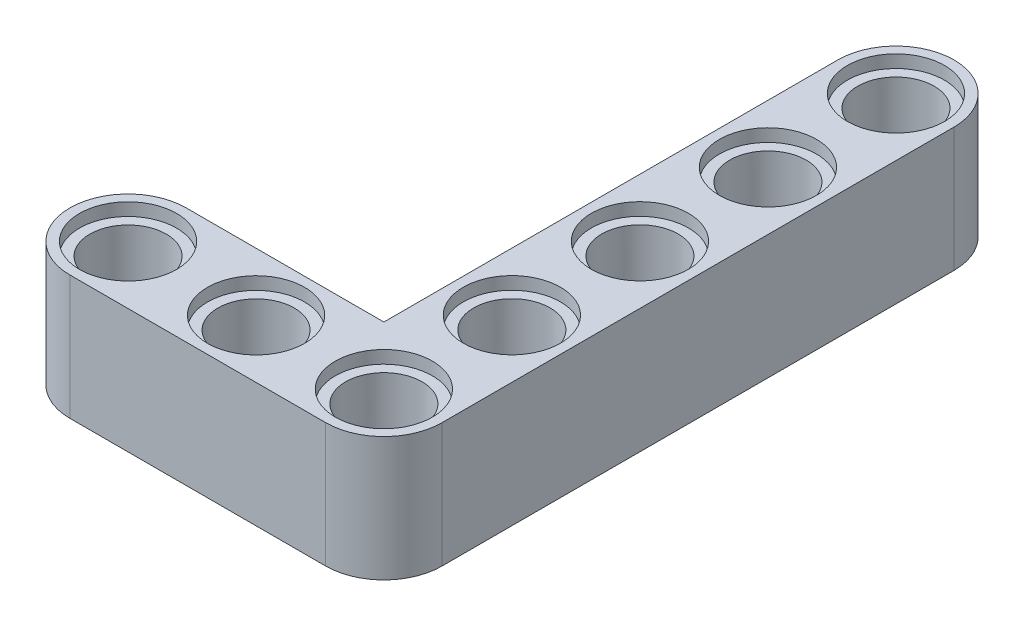
SolidWorks part; units mm, degrees
ref_plane "Front Plane" through (0, 0, 0) normal (0, 0, 1) x (1, 0, 0)
ref_plane "Top Plane" through (0, 0, 0) normal (0, 1, 0) x (1, 0, 0)
ref_plane "Right Plane" through (0, 0, 0) normal (1, 0, 0) x (0, 0, -1)
sketch "Sketch1" plane through (0, 0, 0) normal (0, 1, 0) x (1, 0, 0)
  line L0 (-39.0124, -18.5406) -> (-22.9465, -18.5406) construction
  line L1 (-39.0124, -14.8906) -> (-26.5965, -14.8906)
  line L2 (-39.0124, -22.1906) -> (-22.9465, -22.1906)
  line L3 (-22.9465, -18.5406) -> (-22.9465, 13.6194) construction
  line L4 (-26.5965, -14.8906) -> (-26.5965, 13.6194)
  line L5 (-19.2965, -18.5406) -> (-19.2965, 13.6194)
  line L6 (-22.9465, -10.5006) -> (-14.847, -10.5006) construction
  line L7 (-22.9465, -2.4606) -> (-14.847, -2.4606) construction
  line L8 (-22.9465, 5.5794) -> (-13.347, 5.5794) construction
  arc A0 (-39.0124, -14.8906) -> (-39.0124, -22.1906) centre (-39.0124, -18.5406) ccw
  arc A1 (-22.9465, -22.1906) -> (-19.2965, -18.5406) centre (-22.9465, -18.5406) ccw
  circle A2 centre (-39.0124, -18.5406) radius 2.4
  circle A3 centre (-30.9724, -18.5406) radius 2.4
  circle A4 centre (-22.9465, -18.5406) radius 2.4
  arc A6 (-19.2965, 13.6194) -> (-26.5965, 13.6194) centre (-22.9465, 13.6194) ccw
  circle A7 centre (-22.9465, 13.6194) radius 2.4
  circle A8 centre (-22.9465, 5.5794) radius 2.4
  circle A9 centre (-22.9465, -2.4606) radius 2.4
  circle A10 centre (-22.9465, -10.5006) radius 2.4
  point P2 (-30.9815, -18.5406)
  point P13 (-22.9424, -6.6711)
  dimension "D3" = 8.04
  dimension "D4" = 8.04
  dimension "D1" = 7.3
  dimension "D2" = 8.035
  dimension "D5" = 8.04
  dimension "D6" = 8.04
  dimension "D7" = 8.04
  dimension "D8" = 7.3
extrude "Boss-Extrude1" add sketch "Sketch1" along normal blind 7.8
sketch "Sketch2" plane through (0, 7.8, 0) normal (0, 1, 0) x (1, 0, 0)
  circle A0 centre (-39.0124, -18.5406) radius 3.05
  circle A1 centre (-30.9724, -18.5406) radius 3.05
  circle A2 centre (-22.9465, -18.5406) radius 3.05
  circle A3 centre (-22.9465, -10.5006) radius 3.05
  circle A4 centre (-22.9465, -2.4606) radius 3.05
  circle A5 centre (-22.9465, 5.5794) radius 3.05
  circle A6 centre (-22.9465, 13.6194) radius 3.05
extrude "Cut-Extrude1" cut sketch "Sketch2" against normal blind 0.8
sketch "Sketch3" plane through (0, 0, 0) normal (0, -1, 0) x (1, 0, 0)
  circle A0 centre (-30.9724, 18.5406) radius 3.05
  circle A1 centre (-39.0124, 18.5406) radius 3.05
  circle A2 centre (-22.9465, 18.5406) radius 3.05
  circle A3 centre (-22.9465, 10.5006) radius 3.05
  circle A4 centre (-22.9465, 2.4606) radius 3.05
  circle A5 centre (-22.9465, -5.5794) radius 3.05
  circle A6 centre (-22.9465, -13.6194) radius 3.05
extrude "Cut-Extrude2" cut sketch "Sketch3" against normal blind 0.8
